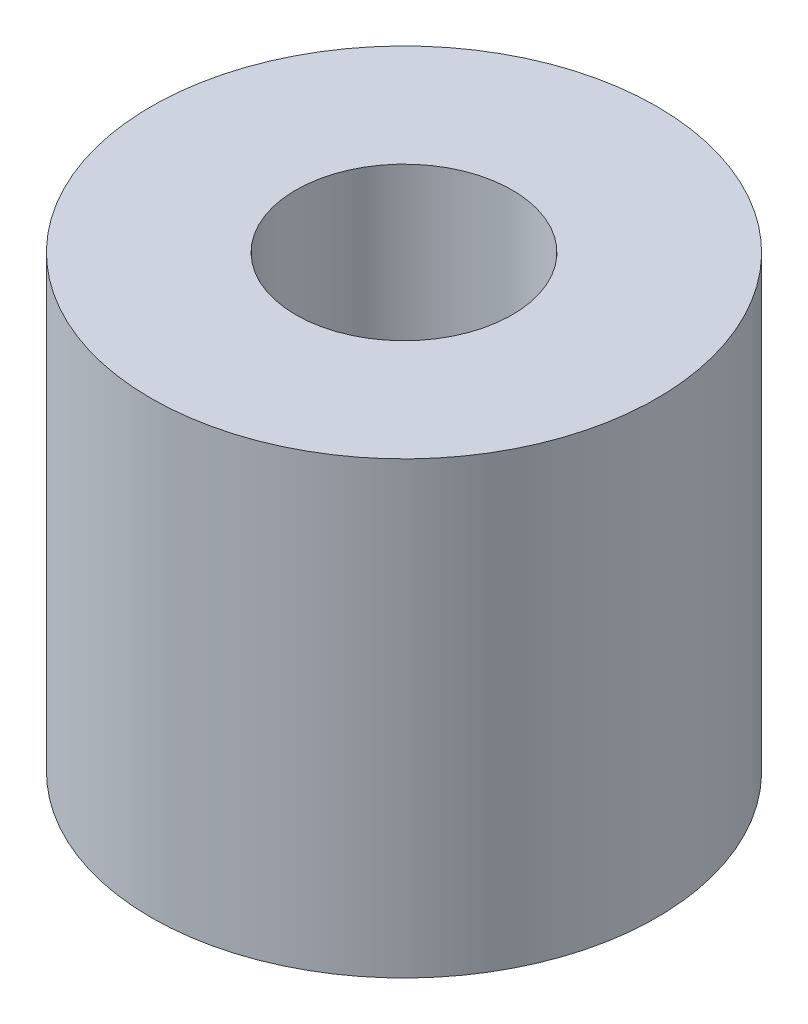
SolidWorks part; units mm, degrees
ref_plane "Front Plane" through (0, 0, 0) normal (0, 0, 1) x (1, 0, 0)
ref_plane "Top Plane" through (0, 0, 0) normal (0, 1, 0) x (1, 0, 0)
ref_plane "Right Plane" through (0, 0, 0) normal (1, 0, 0) x (0, 0, -1)
sketch "Sketch1" plane through (0, 0, 0) normal (0, 1, 0) x (1, 0, 0)
  circle A0 centre (0, 0) radius 50
  circle A1 centre (0, 0) radius 21.39
  dimension "D1" = 100
  dimension "D2" = 42.78
extrude "Boss-Extrude1" add sketch "Sketch1" along normal blind 88.9
